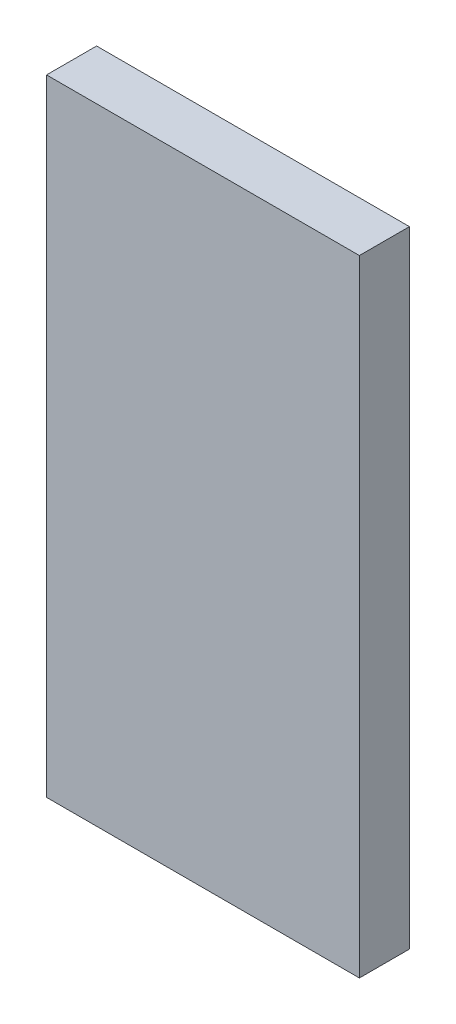
SolidWorks part; units mm, degrees
material "PMMA"
ref_plane "Front Plane" through (0, 0, 0) normal (0, 0, 1) x (1, 0, 0)
ref_plane "Top Plane" through (0, 0, 0) normal (0, 1, 0) x (1, 0, 0)
ref_plane "Right Plane" through (0, 0, 0) normal (1, 0, 0) x (0, 0, -1)
sketch "Sketch1" plane through (0, 0, 0) normal (0, 0, 1) x (1, 0, 0)
  line L1 (-2.5, 5) -> (2.5, 5)
  line L2 (-2.5, 5) -> (-2.5, -5)
  line L3 (-2.5, -5) -> (2.5, -5)
  line L4 (2.5, 5) -> (2.5, -5)
  line L5 (-2.5, 5) -> (2.5, -5) construction
  line L6 (-2.5, -5) -> (2.5, 5) construction
  point P0 (0, 0)
  dimension "D1" = 10
  dimension "D2" = 5
extrude "Boss-Extrude1" add sketch "Sketch1" along normal blind 0.8
